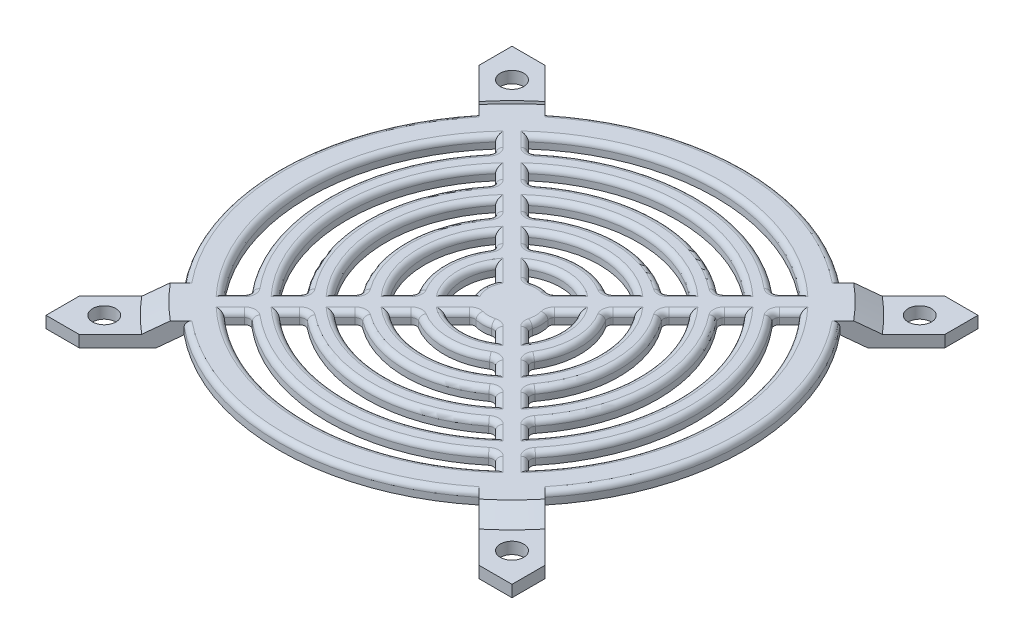
SolidWorks part; units mm, degrees
material "1.6523 (20NiCrMoS2-2)"
ref_plane "Спереди" through (0, 0, 0) normal (0, 0, 1) x (1, 0, 0)
ref_plane "Сверху" through (0, 0, 0) normal (0, 1, 0) x (1, 0, 0)
ref_plane "Справа" through (0, 0, 0) normal (1, 0, 0) x (0, 0, -1)
sketch "Эскиз1" plane through (0, 0, 0) normal (0, 1, 0) x (1, 0, 0)
  line L0 (-51.5147, -60) -> (-37.9711, -46.4564)
  line L1 (-60, 60) -> (-51.5147, 60)
  line L2 (-60, 60) -> (-60, 51.5147)
  line L3 (-60, -60) -> (-51.5147, -60)
  line L4 (60, 60) -> (60, 51.5147)
  line L5 (-60, 60) -> (60, -60) construction
  line L6 (-60, -60) -> (60, 60) construction
  line L7 (-52.5, 52.5) -> (52.5, 52.5) construction
  line L8 (-52.5, 52.5) -> (-52.5, -52.5) construction
  line L9 (-52.5, -52.5) -> (52.5, -52.5) construction
  line L10 (52.5, 52.5) -> (52.5, -52.5) construction
  line L11 (-52.5, 52.5) -> (52.5, -52.5) construction
  line L12 (-52.5, -52.5) -> (52.5, 52.5) construction
  line L13 (-60, -51.5147) -> (-46.4564, -37.9711)
  line L14 (-60, 51.5147) -> (-46.4564, 37.9711)
  line L15 (-51.5147, 60) -> (-37.9711, 46.4564)
  line L16 (14.3125, 10.0699) -> (17.8892, 13.6465)
  line L17 (2.7392, -6.9819) -> (6.4592, -10.7018)
  line L18 (51.5147, 60) -> (60, 60)
  line L19 (6.9819, -2.7392) -> (10.7018, -6.4592)
  line L20 (-60, -51.5147) -> (-60, -60)
  line L21 (6.9819, 2.7392) -> (10.7018, 6.4592)
  line L22 (-64.2426, 55.7574) -> (55.7574, -64.2426) construction
  line L23 (2.7392, 6.9819) -> (6.4592, 10.7018)
  line L24 (10.0699, 14.3125) -> (13.6465, 17.8892)
  line L25 (46.4564, -37.9711) -> (60, -51.5147)
  line L26 (-6.4592, 10.7018) -> (-2.7392, 6.9819)
  line L27 (-10.7018, 6.4592) -> (-6.9819, 2.7392)
  line L28 (-10.7018, -6.4592) -> (-6.9819, -2.7392)
  line L29 (-6.4592, -10.7018) -> (-2.7392, -6.9819)
  line L30 (10.0699, -14.3125) -> (13.6465, -17.8892)
  line L31 (14.3125, -10.0699) -> (17.8892, -13.6465)
  line L32 (21.4507, -17.2081) -> (25.0042, -20.7615)
  line L33 (28.5528, -24.3102) -> (32.0984, -27.8558)
  line L34 (35.6418, -31.3992) -> (39.1838, -34.9411)
  line L35 (17.2081, -21.4507) -> (20.7615, -25.0042)
  line L36 (24.3102, -28.5528) -> (27.8558, -32.0984)
  line L37 (31.3992, -35.6418) -> (34.9411, -39.1838)
  line L38 (-13.6465, -17.8892) -> (-10.0699, -14.3125)
  line L39 (-20.7615, -25.0042) -> (-17.2081, -21.4507)
  line L40 (-27.8558, -32.0984) -> (-24.3102, -28.5528)
  line L41 (-32.0984, -27.8558) -> (-28.5528, -24.3102)
  line L42 (-25.0042, -20.7615) -> (-21.4507, -17.2081)
  line L43 (-17.8892, -13.6465) -> (-14.3125, -10.0699)
  line L44 (-17.8892, 13.6465) -> (-14.3125, 10.0699)
  line L45 (-25.0042, 20.7615) -> (-21.4507, 17.2081)
  line L46 (-32.0984, 27.8558) -> (-28.5528, 24.3102)
  line L47 (-13.6465, 17.8892) -> (-10.0699, 14.3125)
  line L48 (-20.7615, 25.0042) -> (-17.2081, 21.4507)
  line L49 (-27.8558, 32.0984) -> (-24.3102, 28.5528)
  line L50 (21.4507, 17.2081) -> (25.0042, 20.7615)
  line L51 (28.5528, 24.3102) -> (32.0984, 27.8558)
  line L52 (35.6418, 31.3992) -> (39.1838, 34.9411)
  line L53 (31.3992, 35.6418) -> (34.9411, 39.1838)
  line L54 (17.2081, 21.4507) -> (20.7615, 25.0042)
  line L55 (24.3102, 28.5528) -> (27.8558, 32.0984)
  line L56 (-39.1838, 34.9411) -> (-35.6418, 31.3992)
  line L57 (-34.9411, 39.1838) -> (-31.3992, 35.6418)
  line L58 (-55.7574, 64.2426) -> (64.2426, -55.7574) construction
  line L59 (37.9711, -46.4564) -> (51.5147, -60)
  line L60 (-55.7574, -64.2426) -> (64.2426, 55.7574) construction
  line L61 (46.4564, 37.9711) -> (60, 51.5147)
  line L62 (-34.9411, -39.1838) -> (-31.3992, -35.6418)
  line L63 (-39.1838, -34.9411) -> (-35.6418, -31.3992)
  line L64 (-64.2426, -55.7574) -> (55.7574, 64.2426) construction
  line L65 (37.9711, 46.4564) -> (51.5147, 60)
  line L66 (60, -51.5147) -> (60, -60)
  line L67 (51.5147, -60) -> (60, -60)
  arc A0 (-2.7392, -6.9819) -> (2.7392, -6.9819) centre (0, 0) ccw
  arc A1 (-6.4592, -10.7018) -> (6.4592, -10.7018) centre (0, 0) ccw
  arc A2 (-10.0699, -14.3125) -> (10.0699, -14.3125) centre (0, 0) ccw
  arc A3 (-13.6465, -17.8892) -> (13.6465, -17.8892) centre (0, 0) ccw
  arc A4 (-17.2081, -21.4507) -> (17.2081, -21.4507) centre (0, 0) ccw
  arc A5 (-20.7615, -25.0042) -> (20.7615, -25.0042) centre (0, 0) ccw
  arc A6 (-24.3102, -28.5528) -> (24.3102, -28.5528) centre (0, 0) ccw
  arc A7 (-27.8558, -32.0984) -> (27.8558, -32.0984) centre (0, 0) ccw
  arc A8 (-31.3992, -35.6418) -> (31.3992, -35.6418) centre (0, 0) ccw
  arc A9 (-34.9411, -39.1838) -> (34.9411, -39.1838) centre (0, 0) ccw
  circle A10 centre (-52.5, -52.5) radius 3
  circle A11 centre (-52.5, 52.5) radius 3
  circle A12 centre (52.5, 52.5) radius 3
  circle A13 centre (52.5, -52.5) radius 3
  arc A14 (2.7392, 6.9819) -> (-2.7392, 6.9819) centre (0, 0) ccw
  arc A15 (6.4592, 10.7018) -> (-6.4592, 10.7018) centre (0, 0) ccw
  arc A16 (10.0699, 14.3125) -> (-10.0699, 14.3125) centre (0, 0) ccw
  arc A17 (13.6465, 17.8892) -> (-13.6465, 17.8892) centre (0, 0) ccw
  arc A18 (17.2081, 21.4507) -> (-17.2081, 21.4507) centre (0, 0) ccw
  arc A19 (20.7615, 25.0042) -> (-20.7615, 25.0042) centre (0, 0) ccw
  arc A20 (24.3102, 28.5528) -> (-24.3102, 28.5528) centre (0, 0) ccw
  arc A21 (27.8558, 32.0984) -> (-27.8558, 32.0984) centre (0, 0) ccw
  arc A22 (31.3992, 35.6418) -> (-31.3992, 35.6418) centre (0, 0) ccw
  arc A23 (34.9411, 39.1838) -> (-34.9411, 39.1838) centre (0, 0) ccw
  arc A24 (-6.9819, 2.7392) -> (-6.9819, -2.7392) centre (0, 0) ccw
  arc A25 (-10.7018, 6.4592) -> (-10.7018, -6.4592) centre (0, 0) ccw
  arc A26 (-14.3125, 10.0699) -> (-14.3125, -10.0699) centre (0, 0) ccw
  arc A27 (-17.8892, 13.6465) -> (-17.8892, -13.6465) centre (0, 0) ccw
  arc A28 (-21.4507, 17.2081) -> (-21.4507, -17.2081) centre (0, 0) ccw
  arc A29 (-25.0042, 20.7615) -> (-25.0042, -20.7615) centre (0, 0) ccw
  arc A30 (-28.5528, 24.3102) -> (-28.5528, -24.3102) centre (0, 0) ccw
  arc A31 (-32.0984, 27.8558) -> (-32.0984, -27.8558) centre (0, 0) ccw
  arc A32 (-35.6418, 31.3992) -> (-35.6418, -31.3992) centre (0, 0) ccw
  arc A33 (-39.1838, 34.9411) -> (-39.1838, -34.9411) centre (0, 0) ccw
  arc A34 (6.9819, -2.7392) -> (6.9819, 2.7392) centre (0, 0) ccw
  arc A35 (10.7018, -6.4592) -> (10.7018, 6.4592) centre (0, 0) ccw
  arc A36 (14.3125, -10.0699) -> (14.3125, 10.0699) centre (0, 0) ccw
  arc A37 (17.8892, -13.6465) -> (17.8892, 13.6465) centre (0, 0) ccw
  arc A38 (21.4507, -17.2081) -> (21.4507, 17.2081) centre (0, 0) ccw
  arc A39 (25.0042, -20.7615) -> (25.0042, 20.7615) centre (0, 0) ccw
  arc A40 (28.5528, -24.3102) -> (28.5528, 24.3102) centre (0, 0) ccw
  arc A41 (32.0984, -27.8558) -> (32.0984, 27.8558) centre (0, 0) ccw
  arc A42 (35.6418, -31.3992) -> (35.6418, 31.3992) centre (0, 0) ccw
  arc A43 (39.1838, -34.9411) -> (39.1838, 34.9411) centre (0, 0) ccw
  arc A44 (-37.9711, -46.4564) -> (37.9711, -46.4564) centre (0, 0) ccw
  arc A45 (46.4564, -37.9711) -> (46.4564, 37.9711) centre (0, 0) ccw
  arc A46 (37.9711, 46.4564) -> (-37.9711, 46.4564) centre (0, 0) ccw
  arc A47 (-46.4564, 37.9711) -> (-46.4564, -37.9711) centre (0, 0) ccw
  point P0 (0, 0)
  point P25 (-62.1213, 57.8787)
  point P26 (57.8787, -62.1213)
  point P27 (-57.8787, 62.1213)
  point P28 (62.1213, -57.8787)
  point P29 (-57.8787, -62.1213)
  point P30 (62.1213, 57.8787)
  point P31 (-62.1213, -57.8787)
  point P32 (57.8787, 62.1213)
  dimension "D3" = 15
  dimension "D4" = 25
  dimension "D5" = 35
  dimension "D6" = 45
  dimension "D7" = 55
  dimension "D8" = 65
  dimension "D9" = 75
  dimension "D10" = 85
  dimension "D11" = 95
  dimension "D12" = 105
  dimension "D15" = 6
  dimension "D16" = 6
  dimension "D17" = 6
  dimension "D18" = 6
  dimension "D1" = 120
  dimension "D2" = 120
  dimension "D13" = 105
  dimension "D14" = 105
  dimension "D19" = 6
  dimension "D20" = 6
  dimension "D21" = 6
  dimension "D22" = 6
extrude "Бобышка-Вытянуть1" add sketch "Эскиз1" along normal blind 6
sketch "Эскиз2" plane through (0, 0, 0) normal (0, -1, 0) x (1, 0, 0)
  circle A0 centre (0, 0) radius 65
  dimension "D1" = 130
extrude "Вырез-Вытянуть1" cut sketch "Эскиз2" against normal blind 3 draft 60
sketch "Эскиз3" plane through (0, 6, 0) normal (0, 1, 0) x (1, 0, 0)
  circle A0 centre (0, 0) radius 62.5
  dimension "D1" = 125
extrude "Вырез-Вытянуть2" cut sketch "Эскиз3" against normal blind 3 draft 60 flip side to cut
fillet "Скругление1" radius 1.4 81 edges at (0, 6, 47.5) (33.1702, 6, 37.4128) (24.3102, 4.5, 28.5528) (-24.3102, 4.5, 28.5528) (0, 6, 42.5) (-31.3992, 4.5, 35.6418) (-17.2081, 4.5, 21.4507) (-18.9848, 6, 23.2274) (18.9848, 6, 23.2274) (-2.7392, 4.5, 6.9819) (0, 6, 12.5) (4.5992, 6, 8.8418) (0, 6, 7.5) (-4.5992, 6, 8.8418) (-10.0699, 4.5, 14.3125) (-11.8582, 6, 16.1008) (0, 6, 22.5) (11.8582, 6, 16.1008) (0, 6, 17.5) (35.6418, 4.5, 31.3992) (35.6418, 4.5, -31.3992) (28.5528, 4.5, -24.3102) (28.5528, 4.5, 24.3102) (14.3125, 4.5, 10.0699) (6.9819, 4.5, -2.7392) (6.9819, 4.5, 2.7392) (7.5, 6, 0) (32.5, 6, 0) (27.5, 6, 0) (42.5, 6, 0) (23.2274, 6, 18.9848) (16.1008, 6, 11.8582) (8.8418, 6, 4.5992) (23.2274, 6, -18.9848) (37.4128, 6, -33.1702) (0, 6, 60) (60, 6, 0) (31.3992, 4.5, -35.6418) (24.3102, 4.5, -28.5528) (10.0699, 4.5, -14.3125) (-2.7392, 4.5, -6.9819) (-17.2081, 4.5, -21.4507) (-33.1702, 6, -37.4128) (-26.083, 6, -30.3256) (-18.9848, 6, -23.2274) (-11.8582, 6, -16.1008) (18.9848, 6, -23.2274) (26.083, 6, -30.3256) (0, 6, -52.5) (0, 6, -42.5) (0, 6, -32.5) (0, 6, -27.5) (0, 6, -22.5) (0, 6, -17.5) (0, 6, -12.5) (-4.5992, 6, -8.8418) (4.5992, 6, -8.8418) (-30.3256, 6, 26.083) (-23.2274, 6, 18.9848) (-16.1008, 6, 11.8582) (-8.8418, 6, 4.5992) (-8.8418, 6, -4.5992) (-16.1008, 6, -11.8582) (-23.2274, 6, -18.9848) (-30.3256, 6, -26.083) (-52.5, 6, 0) (-47.5, 6, 0) (-42.5, 6, 0) (-37.5, 6, 0) (-27.5, 6, 0) (-22.5, 6, 0) (-12.5, 6, 0) (-7.5, 6, 0) (-14.3125, 4.5, -10.0699) (-21.4507, 4.5, -17.2081) (-28.5528, 4.5, -24.3102) (-14.3125, 4.5, 10.0699) (-21.4507, 4.5, 17.2081) (-28.5528, 4.5, 24.3102) (-35.6418, 4.5, 31.3992) (-37.4128, 6, 33.1702)
